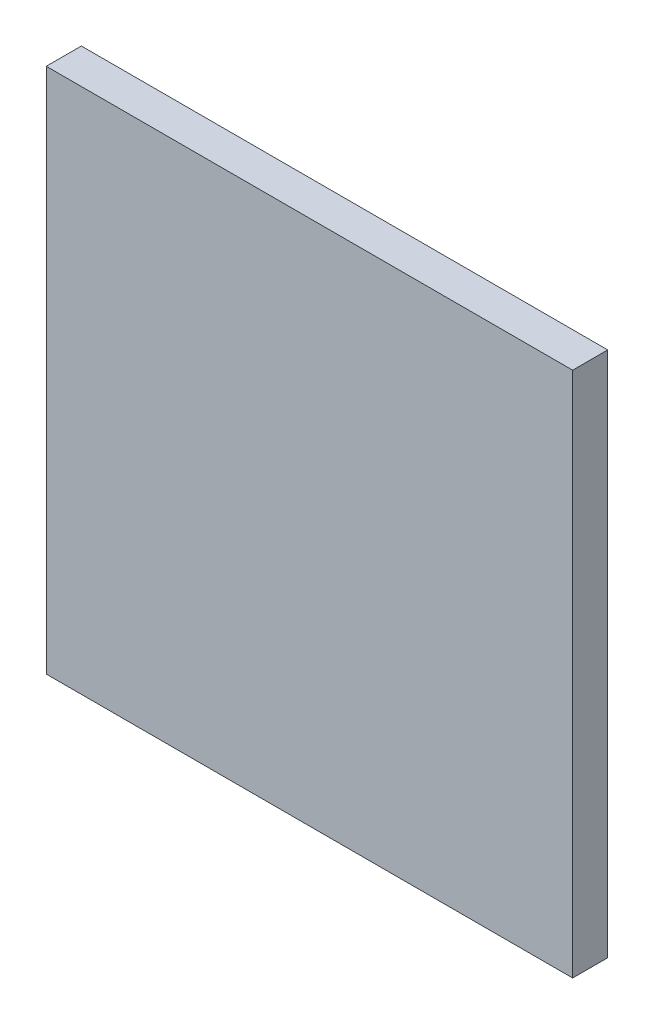
SolidWorks part; units mm, degrees
ref_plane "Plan de face" through (0, 0, 0) normal (0, 0, 1) x (1, 0, 0)
ref_plane "Plan de dessus" through (0, 0, 0) normal (0, 1, 0) x (1, 0, 0)
ref_plane "Plan de droite" through (0, 0, 0) normal (1, 0, 0) x (0, 0, -1)
sketch "Esquisse1" plane through (0, 0, 0) normal (0, 0, 1) x (1, 0, 0)
  line L5 (-15, -15) -> (15, -15)
  line L6 (-15, -15) -> (-15, 15)
  line L7 (-15, 15) -> (15, 15)
  line L8 (15, -15) -> (15, 15)
  line L9 (-15, -15) -> (15, 15) construction
  line L10 (-15, 15) -> (15, -15) construction
  point P0 (0, 0)
  dimension "D1" = 30
  dimension "D2" = 30
extrude "Boss.-Extru.1" add sketch "Esquisse1" along normal blind 2
